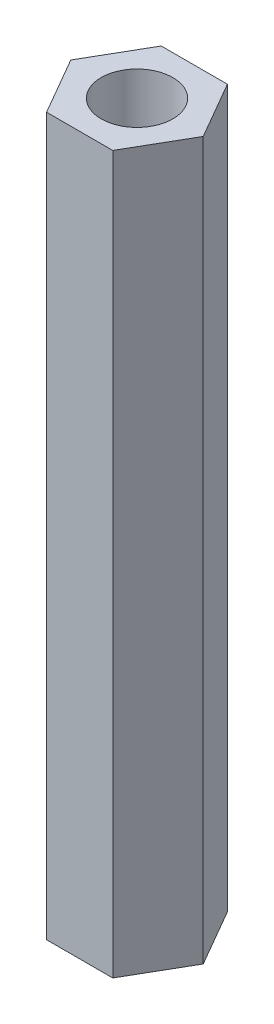
SolidWorks part; units mm, degrees
ref_plane "Front Plane" through (0, 0, 0) normal (0, 0, 1) x (1, 0, 0)
ref_plane "Top Plane" through (0, 0, 0) normal (0, 1, 0) x (1, 0, 0)
ref_plane "Right Plane" through (0, 0, 0) normal (1, 0, 0) x (0, 0, -1)
sketch "Sketch1" plane through (0, 0, 0) normal (0, 1, 0) x (1, 0, 0)
  line L1 (4.6188, 0) -> (2.3094, 4)
  line L2 (2.3094, 4) -> (-2.3094, 4)
  line L3 (-2.3094, 4) -> (-4.6188, 0)
  line L4 (-4.6188, 0) -> (-2.3094, -4)
  line L5 (-2.3094, -4) -> (2.3094, -4)
  line L6 (2.3094, -4) -> (4.6188, 0)
  circle A0 centre (0, 0) radius 2.5
  circle A2 centre (0, 0) radius 4 construction
  point P4 (4.3311, -0.402)
  point P12 (0, 0)
  point P13 (0, 0)
  dimension "D1" = 5
  dimension "D2" = 8
extrude "Boss-Extrude1" add sketch "Sketch1" along normal blind 50
thread "Thread1" pitch 0.8 start angle 0, offset 1, length 0, pitch 0.8, diameter 5
ref_plane "Plane1" through (-2.5, 51, 0) normal (0, 0, 1) x (-1, 0, 0)
sketch "Thread Profile1" plane through (-2.5, 51, 0) normal (0, 0, 1) x (-1, 0, 0)
  line L0 (0, 0) -> (0, 0.8) construction
  line L1 (0, 0) -> (0.433, 0.25)
  line L2 (0.433, 0.25) -> (0.433, 0.35)
  line L3 (0.433, 0.35) -> (0, 0.6)
  line L4 (0.433, 0.3) -> (0, 0.3) construction
  line L11 (0, 0) -> (0, 0.6)
  point P2 (0, 0)
  dimension "Pitch" = 0.8
  dimension "Profile_Angle" = 60
  dimension "Profile_Land" = 0.1
  dimension "Profile_Height" = 0.433
